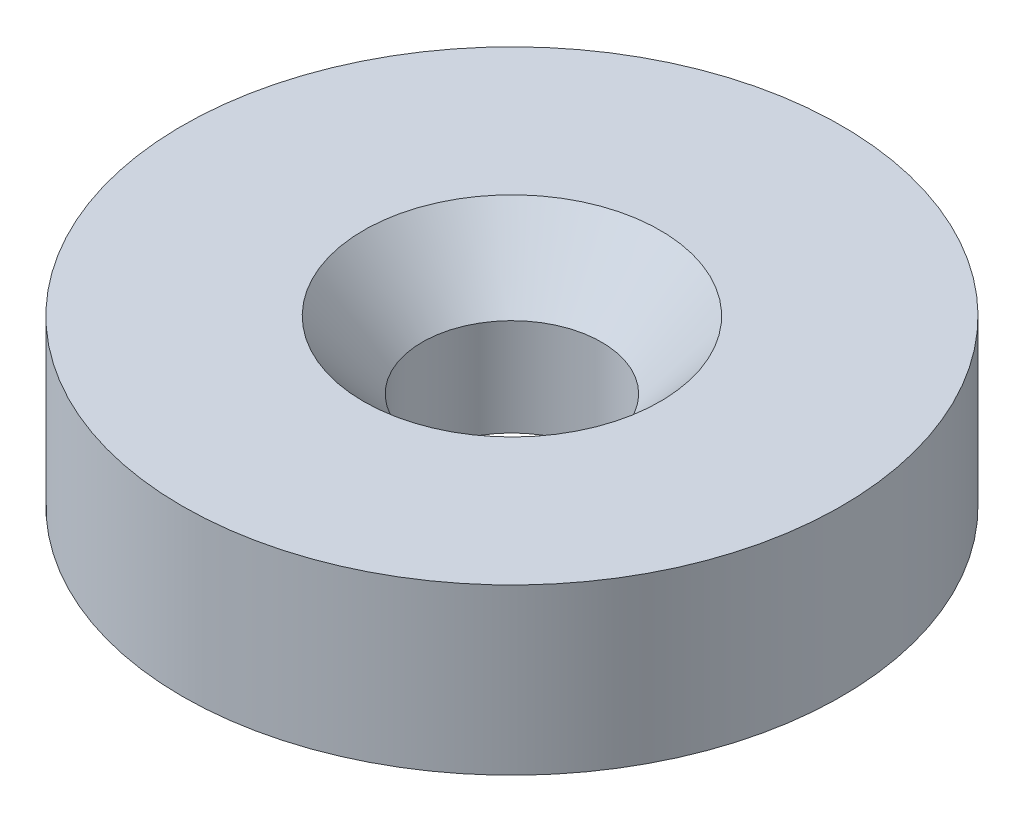
SolidWorks part; units mm, degrees
material "6061-T6 (SS)"
ref_plane "Front Plane" through (0, 0, 0) normal (0, 0, 1) x (1, 0, 0)
ref_plane "Top Plane" through (0, 0, 0) normal (0, 1, 0) x (1, 0, 0)
ref_plane "Right Plane" through (0, 0, 0) normal (1, 0, 0) x (0, 0, -1)
sketch "Sketch1" plane through (0, 0, 0) normal (0, 1, 0) x (1, 0, 0)
  circle A0 centre (0, 0) radius 6.35
  dimension "D1" = 12.7
extrude "Boss-Extrude1" add sketch "Sketch1" along normal blind 3.175
hole_wizard "CSK for #4 Flat Head Machine Screw1" positions "Sketch2" profile "Sketch3" countersink size "#4" standard "ANSI Inch" end condition through all
sketch "Sketch2" plane through (0, 3.175, 0) normal (0, 1, 0) x (1, 0, 0)
  point P0 (0, 0)
sketch "Sketch3" plane through (0, 3.175, 0) normal (1, 0, 0) x (0, 0, 1)
  line L0 (0, 0) -> (0, 3.175)
  line L1 (0, 3.175) -> (1.7272, 3.175)
  line L2 (1.7272, 3.175) -> (1.7272, 1.3003)
  line L3 (1.7272, 1.3003) -> (2.8575, 0)
  line L5 (2.8575, 0) -> (0, 0)
  line L6 (-1.7272, 1.3003) -> (-2.8575, 0) construction
  line L11 (0, -6.35) -> (0, 107.95) construction
  dimension "Thru Hole Dia." = 3.4544
  dimension "Thru Hole Depth" = 3.175
  dimension "Near C'Sink Dia." = 5.715
  dimension "Near C'Sink Angle" = 82
equation "\"Thick\"= \"in\""
